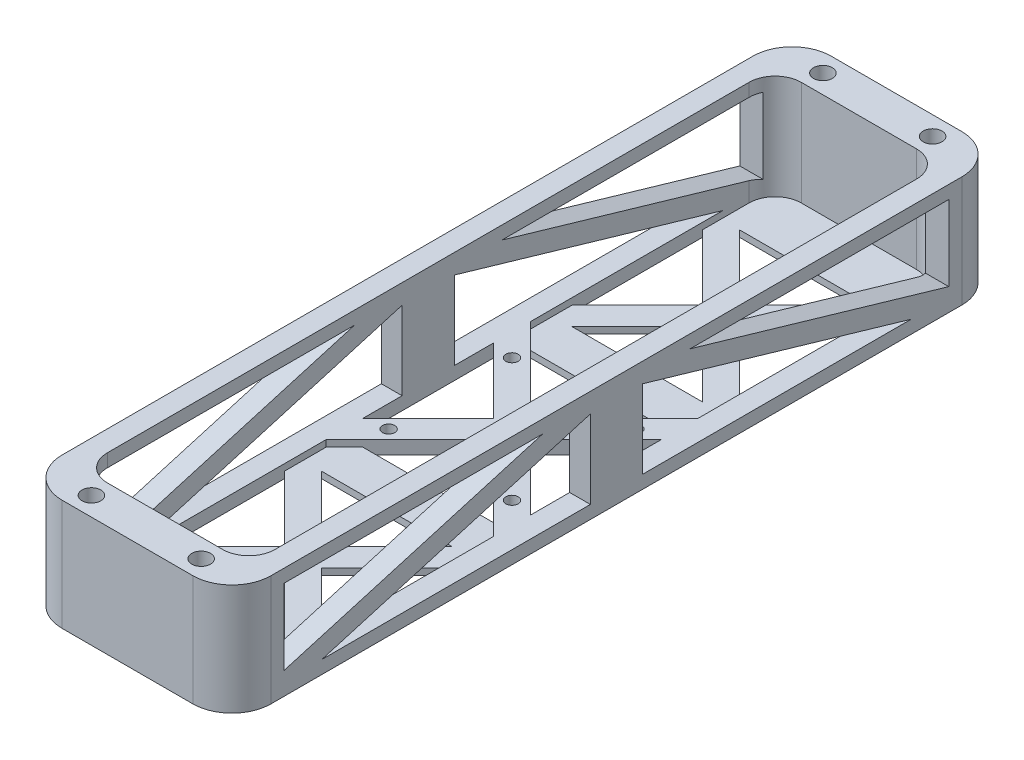
SolidWorks part; units mm, degrees
other "Markup1"
sketch "Sketch7" plane through (101.6, 15.875, -101.6) normal (0.5881, 0.7382, -0.3306) x (-0.8071, 0.509, -0.2992)
ref_plane "Front Plane" through (0, 0, 0) normal (0, 0, 1) x (1, 0, 0)
ref_plane "Top Plane" through (0, 0, 0) normal (0, 1, 0) x (1, 0, 0)
ref_plane "Right Plane" through (0, 0, 0) normal (1, 0, 0) x (0, 0, -1)
sketch "Sketch1" plane through (0, 0, 0) normal (0, 1, 0) x (1, 0, 0)
  line L0 (-25.4, 101.6) -> (25.4, 101.6)
  line L1 (-25.4, -101.6) -> (25.4, -101.6)
  line L2 (-101.6, -25.4) -> (-101.6, 25.4)
  line L3 (-25.4, 101.6) -> (25.4, 101.6)
  line L4 (101.6, -25.4) -> (101.6, 25.4)
  line L5 (-25.4, 101.6) -> (-25.4, 25.4)
  line L6 (-25.4, 25.4) -> (-101.6, 25.4)
  line L7 (101.6, -25.4) -> (101.6, 25.4)
  line L8 (-101.6, -25.4) -> (-101.6, 25.4)
  line L9 (-25.4, -101.6) -> (25.4, -101.6)
  line L10 (-101.6, -25.4) -> (-25.4, -25.4)
  line L11 (-25.4, -25.4) -> (-25.4, -101.6)
  line L12 (25.4, -101.6) -> (25.4, -25.4)
  line L13 (25.4, -25.4) -> (101.6, -25.4)
  line L14 (101.6, 25.4) -> (25.4, 25.4)
  line L15 (25.4, 25.4) -> (25.4, 101.6)
  line L16 (-13.335, 88.9) -> (13.335, 88.9)
  line L17 (88.9, -13.335) -> (88.9, 13.335)
  line L18 (-88.9, -13.335) -> (-88.9, 13.335)
  line L19 (-13.335, -88.9) -> (13.335, -88.9)
  line L21 (-19, -19) -> (19, -19)
  line L22 (-19, -19) -> (-19, 19)
  line L23 (-19, 19) -> (19, 19)
  line L24 (19, -19) -> (19, 19)
  line L25 (-19, -19) -> (19, 19) construction
  line L26 (-19, 19) -> (19, -19) construction
  circle A0 centre (-13.335, 88.9) radius 2.286
  circle A1 centre (13.335, 88.9) radius 2.286
  circle A2 centre (-13.335, -88.9) radius 2.286
  circle A3 centre (13.335, -88.9) radius 2.286
  circle A4 centre (88.9, -13.335) radius 2.286
  circle A5 centre (88.9, 13.335) radius 2.286
  circle A6 centre (-88.9, 13.335) radius 2.286
  circle A7 centre (-88.9, -13.335) radius 2.286
  circle A8 centre (-15, 15) radius 1.5
  circle A9 centre (15, 15) radius 1.5
  circle A10 centre (15, -15) radius 1.5
  circle A11 centre (-15, -15) radius 1.5
  point P0 (0, 0)
  point P6 (0, 101.6)
  point P7 (101.6, 0)
  point P9 (-101.6, 0)
  point P13 (0, 101.6)
  point P16 (101.6, 0)
  point P19 (-101.6, 0)
  point P22 (0, -101.6)
  point P41 (88.9, 0)
  point P43 (0, 0)
  point P44 (-88.9, 0)
  point P47 (0, -88.9)
  point P50 (0, 88.9)
  dimension "D4" = 4.572
  dimension "D14" = 3
  dimension "D1" = 203.2
  dimension "D2" = 50.8
  dimension "D3" = 203.2
  dimension "D5" = 26.67
  dimension "D6" = 12.7
  dimension "D7" = 12.7
  dimension "D8" = 12.7
  dimension "D9" = 12.7
  dimension "D10" = 76.2
  dimension "D11" = 76.2
  dimension "D12" = 38
  dimension "D13" = 4
extrude "Boss-Extrude1" add sketch "Sketch1" along normal blind 1.5875 contours L14 L15 L0 L5 L6 L2 L10 L11 L1 L12 L13 L4 | L21 L24 L23 L22 A11 A10 A9 A8
sketch "Sketch3" plane through (0, 1.5875, 0) normal (0, 1, 0) x (1, 0, 0)
  line L0 (-25.4, 25.4) -> (-25.4, -25.4)
  line L1 (-25.4, -25.4) -> (25.4, -25.4)
  line L2 (25.4, 25.4) -> (25.4, -25.4)
  line L3 (25.4, 25.4) -> (-25.4, 25.4)
  line L4 (-76.2, 25.4) -> (-76.2, -25.4)
  line L5 (-76.2, -25.4) -> (76.2, -25.4)
  line L6 (76.2, -25.4) -> (76.2, 25.4)
  line L7 (25.4, 76.2) -> (-25.4, 76.2)
  line L8 (25.4, -76.2) -> (-25.4, -76.2)
  line L9 (0, 55.2901) -> (-15.875, 71.1651)
  line L10 (0, 55.2901) -> (-4.4901, 50.8)
  line L11 (-4.4901, 50.8) -> (0, 46.3099)
  line L12 (101.6, 25.4) -> (25.4, 25.4)
  line L13 (25.4, 25.4) -> (25.4, 101.6)
  line L14 (25.4, 101.6) -> (-25.4, 101.6)
  line L15 (-25.4, 101.6) -> (-25.4, 25.4)
  line L16 (-25.4, 25.4) -> (-101.6, 25.4)
  line L17 (-101.6, 25.4) -> (-101.6, -25.4)
  line L18 (-101.6, -25.4) -> (-25.4, -25.4)
  line L19 (-25.4, -25.4) -> (-25.4, -101.6)
  line L20 (-25.4, -101.6) -> (25.4, -101.6)
  line L21 (25.4, -101.6) -> (25.4, -25.4)
  line L22 (25.4, -25.4) -> (101.6, -25.4)
  line L23 (101.6, -25.4) -> (101.6, 25.4)
  line L24 (101.6, 25.4) -> (25.4, 25.4)
  line L25 (25.4, 25.4) -> (25.4, 101.6)
  line L26 (25.4, 101.6) -> (-25.4, 101.6)
  line L27 (-25.4, 101.6) -> (-25.4, 25.4)
  line L28 (-25.4, 25.4) -> (-101.6, 25.4)
  line L29 (-101.6, 25.4) -> (-101.6, -25.4)
  line L30 (-101.6, -25.4) -> (-25.4, -25.4)
  line L31 (-25.4, -25.4) -> (-25.4, -101.6)
  line L32 (-25.4, -101.6) -> (25.4, -101.6)
  line L33 (25.4, -101.6) -> (25.4, -25.4)
  line L34 (25.4, -25.4) -> (101.6, -25.4)
  line L35 (101.6, -25.4) -> (101.6, 25.4)
  line L36 (0, 46.3099) -> (4.4901, 50.8)
  line L37 (4.4901, 50.8) -> (0, 55.2901)
  line L38 (-15.875, 71.1651) -> (15.875, 71.1651)
  line L39 (15.875, 71.1651) -> (0, 55.2901)
  line L43 (4.4901, 50.8) -> (20.3651, 66.675)
  line L44 (20.3651, 66.675) -> (20.3651, 34.925)
  line L45 (20.3651, 34.925) -> (4.4901, 50.8)
  line L46 (0, 46.3099) -> (15.875, 30.4349)
  line L47 (15.875, 30.4349) -> (-15.875, 30.4349)
  line L48 (-15.875, 30.4349) -> (0, 46.3099)
  line L49 (-4.4901, 50.8) -> (-20.3651, 34.925)
  line L50 (-20.3651, 34.925) -> (-20.3651, 66.675)
  line L51 (-20.3651, 66.675) -> (-4.4901, 50.8)
  line L52 (55.2901, 0) -> (71.1651, 15.875)
  line L53 (71.1651, 15.875) -> (71.1651, -15.875)
  line L54 (71.1651, -15.875) -> (55.2901, 0)
  line L55 (50.8, 4.4901) -> (34.925, 20.3651)
  line L56 (34.925, 20.3651) -> (66.675, 20.3651)
  line L57 (66.675, 20.3651) -> (50.8, 4.4901)
  line L58 (46.3099, 0) -> (30.4349, -15.875)
  line L59 (30.4349, -15.875) -> (30.4349, 15.875)
  line L60 (30.4349, 15.875) -> (46.3099, 0)
  line L61 (50.8, -4.4901) -> (66.675, -20.3651)
  line L62 (66.675, -20.3651) -> (34.925, -20.3651)
  line L63 (34.925, -20.3651) -> (50.8, -4.4901)
  line L64 (55.2901, 0) -> (50.8, 4.4901)
  line L65 (50.8, 4.4901) -> (46.3099, 0)
  line L66 (46.3099, 0) -> (50.8, -4.4901)
  line L67 (50.8, -4.4901) -> (55.2901, 0)
  line L68 (0, -55.2901) -> (15.875, -71.1651)
  line L69 (15.875, -71.1651) -> (-15.875, -71.1651)
  line L70 (-15.875, -71.1651) -> (0, -55.2901)
  line L71 (4.4901, -50.8) -> (20.3651, -34.925)
  line L72 (20.3651, -34.925) -> (20.3651, -66.675)
  line L73 (20.3651, -66.675) -> (4.4901, -50.8)
  line L74 (0, -46.3099) -> (-15.875, -30.4349)
  line L75 (-15.875, -30.4349) -> (15.875, -30.4349)
  line L76 (15.875, -30.4349) -> (0, -46.3099)
  line L77 (-4.4901, -50.8) -> (-20.3651, -66.675)
  line L78 (-20.3651, -66.675) -> (-20.3651, -34.925)
  line L79 (-20.3651, -34.925) -> (-4.4901, -50.8)
  line L80 (0, -55.2901) -> (4.4901, -50.8)
  line L81 (4.4901, -50.8) -> (0, -46.3099)
  line L82 (0, -46.3099) -> (-4.4901, -50.8)
  line L83 (-4.4901, -50.8) -> (0, -55.2901)
  line L84 (-55.2901, 0) -> (-71.1651, -15.875)
  line L85 (-71.1651, -15.875) -> (-71.1651, 15.875)
  line L86 (-71.1651, 15.875) -> (-55.2901, 0)
  line L87 (-50.8, -4.4901) -> (-34.925, -20.3651)
  line L88 (-34.925, -20.3651) -> (-66.675, -20.3651)
  line L89 (-66.675, -20.3651) -> (-50.8, -4.4901)
  line L90 (-46.3099, 0) -> (-30.4349, 15.875)
  line L91 (-30.4349, 15.875) -> (-30.4349, -15.875)
  line L92 (-30.4349, -15.875) -> (-46.3099, 0)
  line L93 (-50.8, 4.4901) -> (-66.675, 20.3651)
  line L94 (-66.675, 20.3651) -> (-34.925, 20.3651)
  line L95 (-34.925, 20.3651) -> (-50.8, 4.4901)
  line L96 (-55.2901, 0) -> (-50.8, -4.4901)
  line L97 (-50.8, -4.4901) -> (-46.3099, 0)
  line L98 (-46.3099, 0) -> (-50.8, 4.4901)
  line L99 (-50.8, 4.4901) -> (-55.2901, 0)
  line L100 (15.875, 20.3651) -> (0, 4.4901)
  line L101 (0, 4.4901) -> (-4.4901, 0)
  line L102 (4.4901, 0) -> (20.3651, 15.875)
  line L103 (0, -4.4901) -> (4.4901, 0)
  line L104 (-20.3651, -15.875) -> (-20.3651, 15.875)
  line L105 (-20.3651, 15.875) -> (-4.4901, 0)
  line L106 (15.875, -20.3651) -> (-15.875, -20.3651)
  line L107 (-15.875, 20.3651) -> (15.875, 20.3651)
  line L108 (0, -4.4901) -> (15.875, -20.3651)
  line L109 (20.3651, -15.875) -> (4.4901, 0)
  line L110 (20.3651, 15.875) -> (20.3651, -15.875)
  line L111 (4.4901, 0) -> (0, 4.4901)
  line L112 (-4.4901, 0) -> (-20.3651, -15.875)
  line L113 (-4.4901, 0) -> (0, -4.4901)
  line L114 (0, 4.4901) -> (-15.875, 20.3651)
  line L115 (-15.875, -20.3651) -> (0, -4.4901)
  circle A0 centre (0, 50.8) radius 3.175 construction
  circle A1 centre (50.8, 0) radius 3.175 construction
  circle A2 centre (0, -50.8) radius 3.175 construction
  circle A3 centre (-50.8, 0) radius 3.175 construction
  circle A4 centre (0, 0) radius 3.175 construction
  point P18 (-50.8, 0)
  point P20 (0, 50.8)
  point P22 (50.8, 0)
  point P23 (0, -50.8)
  point P24 (-101.6, 0)
  point P25 (0, 101.6)
  point P26 (101.6, 0)
  point P27 (0, -101.6)
  point P48 (0, 50.8)
  point P100 (0, 0)
  dimension "D2" = 25.4
  dimension "D3" = 25.4
  dimension "D4" = 25.4
  dimension "D5" = 25.4
  dimension "D6" = 25.4
  dimension "D7" = 25.4
  dimension "D8" = 25.4
  dimension "D9" = 25.4
  dimension "D10" = 6.35
  dimension "D11" = 31.75
  dimension "D12" = 45
  dimension "D13" = 4
  dimension "D14" = 4
  dimension "D1" = 0
extrude "Cut-Extrude1" cut sketch "Sketch3" against normal up to next contours L39 L38 L9 | L51 L50 L49 | L48 L47 L46 | L45 L44 L43 | L95 L94 L93 | L86 L85 L84 | L89 L88 L87 | L92 L91 L90 | L60 L59 L58 | L57 L56 L55 | L54 L53 L52 | L63 L62 L61 | L76 L75 L74 | L79 L78 L77 | L73 L72 L71 | L70 L69 L68 | L114 L100 L107 | L112 L105 L104 | L115 L106 L108 | L110 L102 L109
sketch "Sketch4" plane through (0, 1.5875, 0) normal (0, 1, 0) x (1, 0, 0)
  line L0 (-93.472, 13.335) -> (-93.472, -13.335)
  line L1 (-84.328, 13.335) -> (-84.328, -13.335)
  line L2 (-93.472, 13.335) -> (-93.472, 25.4)
  line L4 (-93.472, 25.4) -> (-84.328, 25.4)
  line L5 (-84.328, 20.3651) -> (-84.328, 13.335)
  line L6 (-84.328, -13.335) -> (-84.328, -20.3651)
  line L7 (-13.335, -84.328) -> (13.335, -84.328)
  line L8 (-13.335, -93.472) -> (13.335, -93.472)
  line L10 (-84.328, -25.4) -> (-93.472, -25.4)
  line L12 (101.6, 25.4) -> (25.4, 25.4)
  line L13 (25.4, 25.4) -> (25.4, 101.6)
  line L14 (25.4, 101.6) -> (-25.4, 101.6)
  line L15 (-25.4, 101.6) -> (-25.4, 25.4)
  line L16 (-25.4, 25.4) -> (-101.6, 25.4)
  line L17 (-101.6, 25.4) -> (-101.6, -25.4)
  line L18 (-101.6, -25.4) -> (-25.4, -25.4)
  line L19 (-25.4, -25.4) -> (-25.4, -101.6)
  line L20 (-25.4, -101.6) -> (25.4, -101.6)
  line L21 (25.4, -101.6) -> (25.4, -25.4)
  line L22 (25.4, -25.4) -> (101.6, -25.4)
  line L23 (101.6, -25.4) -> (101.6, 25.4)
  line L24 (101.6, 25.4) -> (25.4, 25.4)
  line L25 (25.4, 25.4) -> (25.4, 101.6)
  line L26 (25.4, 101.6) -> (-25.4, 101.6)
  line L27 (-25.4, 101.6) -> (-25.4, 25.4)
  line L28 (-25.4, 25.4) -> (-101.6, 25.4)
  line L29 (-101.6, 25.4) -> (-101.6, -25.4)
  line L30 (-101.6, -25.4) -> (-25.4, -25.4)
  line L31 (-25.4, -25.4) -> (-25.4, -101.6)
  line L32 (-25.4, -101.6) -> (25.4, -101.6)
  line L33 (25.4, -101.6) -> (25.4, -25.4)
  line L34 (25.4, -25.4) -> (101.6, -25.4)
  line L35 (101.6, -25.4) -> (101.6, 25.4)
  line L36 (84.328, -13.335) -> (84.328, 13.335)
  line L37 (93.472, -13.335) -> (93.472, 13.335)
  line L38 (-93.472, -25.4) -> (-93.472, -13.335)
  line L39 (-13.335, 93.472) -> (-25.4, 93.472)
  line L40 (-25.4, 93.472) -> (-25.4, 84.328)
  line L41 (13.335, 84.328) -> (-13.335, 84.328)
  line L42 (13.335, 93.472) -> (-13.335, 93.472)
  line L43 (-20.3651, 84.328) -> (-13.335, 84.328)
  line L44 (13.335, 84.328) -> (20.3651, 84.328)
  line L45 (25.4, 84.328) -> (25.4, 93.472)
  line L46 (25.4, 93.472) -> (13.335, 93.472)
  line L47 (84.328, 13.335) -> (84.328, 20.3651)
  line L48 (84.328, 25.4) -> (93.472, 25.4)
  line L49 (93.472, 25.4) -> (93.472, 13.335)
  line L50 (84.328, 25.4) -> (93.472, 25.4)
  line L51 (93.472, -13.335) -> (93.472, -25.4)
  line L52 (93.472, -25.4) -> (84.328, -25.4)
  line L53 (84.328, -20.3651) -> (84.328, -13.335)
  line L54 (13.335, -93.472) -> (25.4, -93.472)
  line L55 (25.4, -93.472) -> (25.4, -84.328)
  line L56 (20.3651, -84.328) -> (13.335, -84.328)
  line L59 (-13.335, -84.328) -> (-20.3651, -84.328)
  line L60 (-25.4, -84.328) -> (-25.4, -93.472)
  line L61 (-25.4, -93.472) -> (-13.335, -93.472)
  line L62 (20.3651, -34.925) -> (20.3651, -66.675) construction
  line L63 (-20.3651, -66.675) -> (-20.3651, -34.925) construction
  line L64 (-20.3651, 34.925) -> (-20.3651, 66.675) construction
  line L65 (20.3651, 66.675) -> (20.3651, 34.925) construction
  line L66 (34.925, 20.3651) -> (66.675, 20.3651) construction
  line L67 (66.675, -20.3651) -> (34.925, -20.3651) construction
  line L68 (-34.925, -20.3651) -> (-66.675, -20.3651) construction
  line L69 (-66.675, 20.3651) -> (-34.925, 20.3651) construction
  line L70 (20.3651, -34.925) -> (20.3651, -66.675)
  line L71 (-20.3651, -66.675) -> (-20.3651, -34.925)
  line L72 (-20.3651, 34.925) -> (-20.3651, 66.675)
  line L73 (20.3651, 66.675) -> (20.3651, 34.925)
  line L74 (34.925, 20.3651) -> (66.675, 20.3651)
  line L75 (66.675, -20.3651) -> (34.925, -20.3651)
  line L76 (-34.925, -20.3651) -> (-66.675, -20.3651)
  line L77 (-66.675, 20.3651) -> (-34.925, 20.3651)
  line L78 (-25.4, 20.3651) -> (-34.925, 20.3651)
  line L79 (-66.675, 20.3651) -> (-84.328, 20.3651)
  line L80 (-25.4, -20.3651) -> (-20.3651, -20.3651)
  line L81 (-20.3651, -20.3651) -> (-20.3651, -25.4)
  line L82 (-20.3651, 25.4) -> (-20.3651, 34.925)
  line L83 (-20.3651, 66.675) -> (-20.3651, 84.328)
  line L84 (20.3651, 84.328) -> (20.3651, 66.675)
  line L85 (20.3651, 34.925) -> (20.3651, 25.4)
  line L86 (20.3651, -25.4) -> (20.3651, -20.3651)
  line L87 (20.3651, -20.3651) -> (25.4, -20.3651)
  line L88 (25.4, 20.3651) -> (34.925, 20.3651)
  line L89 (66.675, 20.3651) -> (84.328, 20.3651)
  line L90 (84.328, -20.3651) -> (66.675, -20.3651)
  line L91 (34.925, -20.3651) -> (25.4, -20.3651)
  line L92 (20.3651, 25.4) -> (20.3651, 20.3651)
  line L93 (20.3651, -34.925) -> (20.3651, -25.4)
  line L94 (20.3651, 20.3651) -> (25.4, 20.3651)
  line L95 (20.3651, -66.675) -> (20.3651, -84.328)
  line L96 (-20.3651, -66.675) -> (-20.3651, -84.328)
  line L97 (-20.3651, -34.925) -> (-20.3651, -25.4)
  line L98 (-25.4, 20.3651) -> (-20.3651, 20.3651)
  line L99 (-20.3651, 20.3651) -> (-20.3651, 25.4)
  line L100 (-25.4, -20.3651) -> (-34.925, -20.3651)
  line L101 (-66.675, -20.3651) -> (-84.328, -20.3651)
  circle A0 centre (-88.9, -13.335) radius 2.286 construction
  circle A1 centre (-88.9, 13.335) radius 2.286 construction
  circle A2 centre (-88.9, -13.335) radius 2.286
  circle A3 centre (-88.9, 13.335) radius 2.286
  circle A7 centre (13.335, -88.9) radius 2.286
  circle A9 centre (-13.335, -88.9) radius 2.286
  arc A10 (93.472, 13.335) -> (84.328, 13.335) centre (88.9, 13.335) ccw
  circle A11 centre (88.9, 13.335) radius 2.286
  circle A13 centre (88.9, -13.335) radius 2.286
  circle A15 centre (-13.335, 88.9) radius 2.286
  circle A17 centre (13.335, 88.9) radius 2.286
  point P28 (0, 0)
  point P75 (0, 0)
  dimension "D1" = 0
  dimension "D4" = 4
extrude "Boss-Extrude4" add sketch "Sketch4" along normal blind 25.4
sketch "Sketch16" plane through (0, 1.5875, 0) normal (0, 1, 0) x (1, 0, 0)
  line L0 (15.875, 20.3651) -> (0, 4.4901) construction
  line L1 (0, 4.4901) -> (-15.875, 20.3651) construction
  line L2 (-15.875, 20.3651) -> (15.875, 20.3651) construction
  line L3 (20.3651, 15.875) -> (20.3651, -15.875) construction
  line L4 (4.4901, 0) -> (20.3651, 15.875) construction
  line L5 (20.3651, -15.875) -> (4.4901, 0) construction
  line L6 (15.875, -20.3651) -> (-15.875, -20.3651) construction
  line L7 (0, -4.4901) -> (15.875, -20.3651) construction
  line L8 (-15.875, -20.3651) -> (0, -4.4901) construction
  line L9 (-4.4901, 0) -> (-20.3651, -15.875) construction
  line L10 (-20.3651, -15.875) -> (-20.3651, 15.875) construction
  line L11 (-20.3651, 15.875) -> (-4.4901, 0) construction
  line L12 (15.875, 20.3651) -> (0, 4.4901)
  line L13 (0, 4.4901) -> (-15.875, 20.3651)
  line L14 (-15.875, 20.3651) -> (15.875, 20.3651)
  line L15 (20.3651, 15.875) -> (20.3651, -15.875)
  line L16 (4.4901, 0) -> (20.3651, 15.875)
  line L17 (20.3651, -15.875) -> (4.4901, 0)
  line L18 (15.875, -20.3651) -> (-15.875, -20.3651)
  line L19 (0, -4.4901) -> (15.875, -20.3651)
  line L20 (-15.875, -20.3651) -> (0, -4.4901)
  line L21 (-4.4901, 0) -> (-20.3651, -15.875)
  line L22 (-20.3651, -15.875) -> (-20.3651, 15.875)
  line L23 (-20.3651, 15.875) -> (-4.4901, 0)
  line L24 (-20.3651, 15.875) -> (-24.8553, 20.3651)
  line L25 (-15.875, 20.3651) -> (-20.3651, 24.8553)
  line L26 (15.875, 20.3651) -> (20.3651, 24.8553)
  line L27 (20.3651, 15.875) -> (24.8553, 20.3651)
  line L28 (15.875, -20.3651) -> (20.3651, -24.8553)
  line L29 (20.3651, -15.875) -> (24.8553, -20.3651)
  line L30 (-20.3651, -15.875) -> (-24.8553, -20.3651)
  line L31 (-15.875, -20.3651) -> (-20.3651, -24.8553)
  line L36 (84.328, -20.3651) -> (84.328, 20.3651)
  line L38 (84.328, -20.3651) -> (84.328, 20.3651)
  line L40 (84.328, 20.3651) -> (66.675, 20.3651)
  line L42 (84.328, 20.3651) -> (66.675, 20.3651)
  line L44 (66.675, 20.3651) -> (50.8, 4.4901)
  line L46 (66.675, 20.3651) -> (50.8, 4.4901)
  line L48 (50.8, 4.4901) -> (34.925, 20.3651)
  line L50 (50.8, 4.4901) -> (34.925, 20.3651)
  line L52 (34.925, 20.3651) -> (20.3651, 20.3651)
  line L54 (34.925, 20.3651) -> (20.3651, 20.3651)
  line L56 (20.3651, 20.3651) -> (20.3651, 34.925)
  line L58 (20.3651, 20.3651) -> (20.3651, 34.925)
  line L128 (20.3651, 34.925) -> (4.4901, 50.8)
  line L129 (20.3651, 34.925) -> (4.4901, 50.8)
  line L130 (4.4901, 50.8) -> (20.3651, 66.675)
  line L131 (4.4901, 50.8) -> (20.3651, 66.675)
  line L132 (20.3651, 66.675) -> (20.3651, 84.328)
  line L133 (20.3651, 66.675) -> (20.3651, 84.328)
  line L134 (20.3651, 84.328) -> (-20.3651, 84.328)
  line L135 (20.3651, 84.328) -> (-20.3651, 84.328)
  line L136 (-20.3651, 84.328) -> (-20.3651, 66.675)
  line L137 (-20.3651, 84.328) -> (-20.3651, 66.675)
  line L138 (-20.3651, 66.675) -> (-4.4901, 50.8)
  line L139 (-20.3651, 66.675) -> (-4.4901, 50.8)
  line L140 (-4.4901, 50.8) -> (-20.3651, 34.925)
  line L141 (-4.4901, 50.8) -> (-20.3651, 34.925)
  line L142 (-20.3651, 34.925) -> (-20.3651, 20.3651)
  line L143 (-20.3651, 34.925) -> (-20.3651, 20.3651)
  line L144 (-20.3651, 20.3651) -> (-34.925, 20.3651)
  line L145 (-20.3651, 20.3651) -> (-34.925, 20.3651)
  line L146 (-34.925, 20.3651) -> (-50.8, 4.4901)
  line L147 (-34.925, 20.3651) -> (-50.8, 4.4901)
  line L148 (-50.8, 4.4901) -> (-66.675, 20.3651)
  line L149 (-50.8, 4.4901) -> (-66.675, 20.3651)
  line L150 (-66.675, 20.3651) -> (-84.328, 20.3651)
  line L151 (-66.675, 20.3651) -> (-84.328, 20.3651)
  line L152 (-84.328, 20.3651) -> (-84.328, -20.3651)
  line L153 (-84.328, 20.3651) -> (-84.328, -20.3651)
  line L154 (-84.328, -20.3651) -> (-66.675, -20.3651)
  line L155 (-84.328, -20.3651) -> (-66.675, -20.3651)
  line L156 (-66.675, -20.3651) -> (-50.8, -4.4901)
  line L157 (-66.675, -20.3651) -> (-50.8, -4.4901)
  line L158 (-50.8, -4.4901) -> (-34.925, -20.3651)
  line L159 (-50.8, -4.4901) -> (-34.925, -20.3651)
  line L160 (-34.925, -20.3651) -> (-20.3651, -20.3651)
  line L161 (-34.925, -20.3651) -> (-20.3651, -20.3651)
  line L162 (-20.3651, -20.3651) -> (-20.3651, -34.925)
  line L163 (-20.3651, -20.3651) -> (-20.3651, -34.925)
  line L164 (-20.3651, -34.925) -> (-4.4901, -50.8)
  line L165 (-20.3651, -34.925) -> (-4.4901, -50.8)
  line L166 (-4.4901, -50.8) -> (-20.3651, -66.675)
  line L167 (-4.4901, -50.8) -> (-20.3651, -66.675)
  line L168 (-20.3651, -66.675) -> (-20.3651, -84.328)
  line L169 (-20.3651, -66.675) -> (-20.3651, -84.328)
  line L170 (-20.3651, -84.328) -> (20.3651, -84.328)
  line L171 (-20.3651, -84.328) -> (20.3651, -84.328)
  line L172 (20.3651, -84.328) -> (20.3651, -66.675)
  line L173 (20.3651, -84.328) -> (20.3651, -66.675)
  line L174 (20.3651, -66.675) -> (4.4901, -50.8)
  line L175 (20.3651, -66.675) -> (4.4901, -50.8)
  line L176 (4.4901, -50.8) -> (20.3651, -34.925)
  line L177 (4.4901, -50.8) -> (20.3651, -34.925)
  line L178 (20.3651, -34.925) -> (20.3651, -20.3651)
  line L179 (20.3651, -34.925) -> (20.3651, -20.3651)
  line L180 (20.3651, -20.3651) -> (34.925, -20.3651)
  line L181 (20.3651, -20.3651) -> (34.925, -20.3651)
  line L182 (34.925, -20.3651) -> (50.8, -4.4901)
  line L183 (34.925, -20.3651) -> (50.8, -4.4901)
  line L184 (50.8, -4.4901) -> (66.675, -20.3651)
  line L185 (50.8, -4.4901) -> (66.675, -20.3651)
  line L186 (66.675, -20.3651) -> (84.328, -20.3651)
  line L187 (66.675, -20.3651) -> (84.328, -20.3651)
  circle A0 centre (-15, 15) radius 1.5 construction
  circle A1 centre (-15, -15) radius 1.5 construction
  circle A2 centre (15, -15) radius 1.5 construction
  circle A3 centre (15, 15) radius 1.5 construction
  circle A4 centre (-15, 15) radius 1.5
  circle A5 centre (-15, -15) radius 1.5
  circle A6 centre (15, -15) radius 1.5
  circle A7 centre (15, 15) radius 1.5
  dimension "D1" = 0
extrude "Boss-Extrude6" add sketch "Sketch16" along normal blind 1.5875 contours L179 L181 L29 L17 L16 L27 L54 L58 L26 L12 L13 L25 L143 L145 L24 L23 L21 L30 L161 L163 L31 L20 L19 L28
sketch "Sketch17" plane through (0, 26.9875, 0) normal (0, 1, 0) x (1, 0, 0)
  line L0 (-20.3651, -20.3651) -> (-20.3651, -84.328) construction
  line L1 (-84.328, -20.3651) -> (-20.3651, -20.3651) construction
  line L2 (84.328, -20.3651) -> (20.3651, -20.3651) construction
  line L3 (20.3651, -84.328) -> (20.3651, -20.3651) construction
  line L4 (20.3651, 84.328) -> (20.3651, 20.3651) construction
  line L5 (20.3651, 20.3651) -> (84.328, 20.3651) construction
  line L6 (-20.3651, 20.3651) -> (-20.3651, 84.328) construction
  line L7 (-20.3651, 20.3651) -> (-84.328, 20.3651) construction
  line L8 (-4.4901, 0) -> (-24.8553, -20.3651) construction
  line L9 (0, -4.4901) -> (-20.3651, -24.8553) construction
  line L10 (0, -4.4901) -> (20.3651, -24.8553) construction
  line L11 (4.4901, 0) -> (24.8553, -20.3651) construction
  line L12 (-25.4, -25.4) -> (-25.4, -93.472)
  line L13 (-25.4, -93.472) -> (25.4, -93.472)
  line L14 (25.4, -93.472) -> (25.4, -25.4)
  line L15 (25.4, -25.4) -> (93.472, -25.4)
  line L16 (93.472, -25.4) -> (93.472, 25.4)
  line L17 (93.472, 25.4) -> (25.4, 25.4)
  line L18 (25.4, 25.4) -> (25.4, 93.472)
  line L19 (25.4, 93.472) -> (-25.4, 93.472)
  line L20 (-25.4, 93.472) -> (-25.4, 25.4)
  line L21 (-25.4, 25.4) -> (-93.472, 25.4)
  line L22 (-93.472, 25.4) -> (-93.472, -25.4)
  line L23 (-93.472, -25.4) -> (-25.4, -25.4)
  line L24 (-25.4, -25.4) -> (-25.4, -93.472)
  line L25 (-25.4, -93.472) -> (25.4, -93.472)
  line L26 (25.4, -93.472) -> (25.4, -25.4)
  line L27 (25.4, -25.4) -> (93.472, -25.4)
  line L28 (93.472, -25.4) -> (93.472, 25.4)
  line L29 (93.472, 25.4) -> (25.4, 25.4)
  line L30 (25.4, 25.4) -> (25.4, 93.472)
  line L31 (25.4, 93.472) -> (-25.4, 93.472)
  line L32 (-25.4, 93.472) -> (-25.4, 25.4)
  line L33 (-25.4, 25.4) -> (-93.472, 25.4)
  line L34 (-93.472, 25.4) -> (-93.472, -25.4)
  line L35 (-93.472, -25.4) -> (-25.4, -25.4)
  line L36 (4.4901, 0) -> (24.8553, 20.3651) construction
  line L37 (0, 4.4901) -> (20.3651, 24.8553) construction
  line L38 (0, 4.4901) -> (-20.3651, 24.8553) construction
  line L39 (-4.4901, 0) -> (-24.8553, 20.3651) construction
  line L40 (-20.3651, -20.3651) -> (-20.3651, -84.328)
  line L41 (-84.328, -20.3651) -> (-20.3651, -20.3651)
  line L42 (84.328, -20.3651) -> (20.3651, -20.3651)
  line L43 (20.3651, -84.328) -> (20.3651, -20.3651)
  line L44 (20.3651, 84.328) -> (20.3651, 20.3651)
  line L45 (20.3651, 20.3651) -> (84.328, 20.3651)
  line L46 (-20.3651, 20.3651) -> (-20.3651, 84.328)
  line L47 (-20.3651, 20.3651) -> (-84.328, 20.3651)
  line L48 (-4.4901, 0) -> (-24.8553, -20.3651)
  line L49 (0, -4.4901) -> (-20.3651, -24.8553)
  line L50 (0, -4.4901) -> (20.3651, -24.8553)
  line L51 (4.4901, 0) -> (24.8553, -20.3651)
  line L52 (4.4901, 0) -> (24.8553, 20.3651)
  line L53 (0, 4.4901) -> (20.3651, 24.8553)
  line L54 (0, 4.4901) -> (-20.3651, 24.8553)
  line L55 (-4.4901, 0) -> (-24.8553, 20.3651)
  line L56 (-24.8553, 20.3651) -> (-29.8901, 25.4)
  line L57 (-20.3651, 24.8553) -> (-25.4, 29.8901)
  line L58 (20.3651, 24.8553) -> (25.4, 29.8901)
  line L59 (24.8553, 20.3651) -> (29.8901, 25.4)
  line L60 (24.8553, -20.3651) -> (29.8901, -25.4)
  line L61 (20.3651, -24.8553) -> (25.4, -29.8901)
  line L62 (-24.8553, -20.3651) -> (-29.8901, -25.4)
  line L63 (-20.3651, -24.8553) -> (-25.4, -29.8901)
  line L64 (-29.8901, 25.4) -> (-29.8901, 20.3651)
  line L65 (-29.8901, 20.3651) -> (-24.8553, 20.3651)
  line L66 (-25.4, 29.8901) -> (-20.3651, 29.8901)
  line L67 (-20.3651, 29.8901) -> (-20.3651, 24.8553)
  line L68 (25.4, 29.8901) -> (20.3651, 29.8901)
  line L69 (20.3651, 29.8901) -> (20.3651, 24.8553)
  line L70 (24.8553, 20.3651) -> (29.8901, 20.3651)
  line L71 (29.8901, 20.3651) -> (29.8901, 25.4)
  line L72 (25.4, -29.8901) -> (20.3651, -29.8901)
  line L73 (20.3651, -29.8901) -> (20.3651, -24.8553)
  line L74 (24.8553, -20.3651) -> (29.8901, -20.3651)
  line L75 (29.8901, -20.3651) -> (29.8901, -25.4)
  line L76 (-24.8553, -20.3651) -> (-29.8901, -20.3651)
  line L77 (-29.8901, -20.3651) -> (-29.8901, -25.4)
  line L78 (-25.4, -29.8901) -> (-20.3651, -29.8901)
  line L79 (-20.3651, -29.8901) -> (-20.3651, -24.8553)
  line M23 (20.3651, 20.3651) -> (84.328, 20.3651)
  line M26 (20.3651, -20.3651) -> (20.3651, -84.328)
  line M29 (-20.3651, -20.3651) -> (-84.328, -20.3651)
  line M32 (-20.3651, 20.3651) -> (-20.3651, 84.328)
  line M43 (-25.4, -25.4) -> (-25.4, -93.472)
  line M46 (25.4, -25.4) -> (93.472, -25.4)
  line M49 (25.4, 25.4) -> (25.4, 93.472)
  line M52 (-25.4, 25.4) -> (-93.472, 25.4)
  dimension "D1" = 0
extrude "Cut-Extrude13" cut sketch "Sketch17" against normal up to surface (23.8125 mm away) contours L57 L32 L56 L47 M32 M52 | L59 L29 L58 L44 M23 M49 | L61 L26 L60 L42 M26 M46 | L63 L40 L62 L35 M29 M43 | L56 L64 L47 | L66 L57 L46 | L58 L68 L44 | L45 L71 L59 | L75 L42 L60 | L72 L61 L43 | L63 L78 L40 | L41 L77 L62 up to face at (15, 3.175, -13.5)
sketch "Sketch18" plane through (0, 0, 25.4) normal (0, 0, 1) x (1, 0, 0)
  line L0 (84.328, 26.9875) -> (84.328, 1.5875) construction
  line L1 (-84.328, 26.9875) -> (-84.328, 1.5875) construction
  line L2 (84.328, 26.9875) -> (84.328, 1.5875)
  line L3 (-84.328, 26.9875) -> (-84.328, 1.5875)
  line L4 (-25.4, 1.5875) -> (25.4, 1.5875) construction
  line L8 (-25.4, 3.175) -> (-29.8901, 3.175)
  line L9 (-29.8901, 3.175) -> (-29.8901, 26.9875)
  line L10 (-29.8901, 26.9875) -> (-93.472, 26.9875)
  line L11 (-93.472, 26.9875) -> (-93.472, 1.5875)
  line L12 (-93.472, 1.5875) -> (-101.6, 1.5875)
  line L13 (-101.6, 1.5875) -> (-101.6, 0)
  line L14 (-101.6, 0) -> (-25.4, 0)
  line L15 (-25.4, 0) -> (-25.4, 3.175)
  line L16 (-25.4, 3.175) -> (-29.8901, 3.175)
  line L17 (-29.8901, 3.175) -> (-29.8901, 26.9875)
  line L18 (-29.8901, 26.9875) -> (-93.472, 26.9875)
  line L19 (-93.472, 26.9875) -> (-93.472, 1.5875)
  line L20 (-93.472, 1.5875) -> (-101.6, 1.5875)
  line L21 (-101.6, 1.5875) -> (-101.6, 0)
  line L22 (-101.6, 0) -> (-25.4, 0)
  line L23 (-25.4, 0) -> (-25.4, 3.175)
  line L24 (29.8901, 26.9875) -> (29.8901, 3.175)
  line L25 (29.8901, 3.175) -> (25.4, 3.175)
  line L26 (25.4, 3.175) -> (25.4, 0)
  line L27 (25.4, 0) -> (101.6, 0)
  line L28 (101.6, 0) -> (101.6, 1.5875)
  line L29 (101.6, 1.5875) -> (93.472, 1.5875)
  line L30 (93.472, 1.5875) -> (93.472, 26.9875)
  line L31 (93.472, 26.9875) -> (29.8901, 26.9875)
  line L32 (29.8901, 26.9875) -> (29.8901, 3.175)
  line L33 (29.8901, 3.175) -> (25.4, 3.175)
  line L34 (25.4, 3.175) -> (25.4, 0)
  line L35 (25.4, 0) -> (101.6, 0)
  line L36 (101.6, 0) -> (101.6, 1.5875)
  line L37 (101.6, 1.5875) -> (93.472, 1.5875)
  line L38 (93.472, 1.5875) -> (93.472, 26.9875)
  line L39 (93.472, 26.9875) -> (29.8901, 26.9875)
  spline S0 degree 2 poles (-77.978, 26.9875) (0.0091, -28.8428) (77.978, 26.9875) knots 0 0 0 1 1 1
  point P18 (-77.978, 26.9875)
  point P20 (77.978, 26.9875)
  point P22 (0, 1.5875)
  point P23 (0.04, -0.9276)
  point P28 (-29.8901, 3.175)
  dimension "D3" = 6.35
  dimension "D4" = 6.35
  dimension "D1" = 0
  dimension "D2" = 0
extrude "Cut-Extrude15" cut sketch "Sketch18" against normal up to surface (50.8 mm away) contours L1 S0 L0
sketch "Sketch20" plane through (0, 1.5875, 0) normal (0, 1, 0) x (1, 0, 0)
  line L0 (-93.472, -25.4) -> (-93.472, 25.4) construction
  line L1 (-93.472, 25.4) -> (-101.6, 25.4) construction
  line L2 (-101.6, 25.4) -> (-101.6, -25.4) construction
  line L3 (-101.6, -25.4) -> (-93.472, -25.4) construction
  line L4 (-25.4, 101.6) -> (-25.4, 93.472)
  line L5 (-25.4, 93.472) -> (25.4, 93.472)
  line L6 (25.4, 93.472) -> (25.4, 101.6)
  line L7 (25.4, 101.6) -> (-25.4, 101.6)
  line L8 (-25.4, 101.6) -> (-25.4, 93.472)
  line L9 (-25.4, 93.472) -> (25.4, 93.472)
  line L10 (25.4, 93.472) -> (25.4, 101.6)
  line L11 (25.4, 101.6) -> (-25.4, 101.6)
  line L12 (25.4, -101.6) -> (25.4, -93.472) construction
  line L13 (25.4, -93.472) -> (-25.4, -93.472) construction
  line L14 (-25.4, -93.472) -> (-25.4, -101.6) construction
  line L15 (-25.4, -101.6) -> (25.4, -101.6) construction
  line L16 (93.472, 25.4) -> (93.472, -25.4) construction
  line L17 (93.472, -25.4) -> (101.6, -25.4) construction
  line L18 (101.6, -25.4) -> (101.6, 25.4) construction
  line L19 (101.6, 25.4) -> (93.472, 25.4) construction
  line L20 (-93.472, -25.4) -> (-93.472, 25.4)
  line L21 (-93.472, 25.4) -> (-101.6, 25.4)
  line L22 (-101.6, 25.4) -> (-101.6, -25.4)
  line L23 (-101.6, -25.4) -> (-93.472, -25.4)
  line L24 (25.4, -101.6) -> (25.4, -93.472)
  line L25 (25.4, -93.472) -> (-25.4, -93.472)
  line L26 (-25.4, -93.472) -> (-25.4, -101.6)
  line L27 (-25.4, -101.6) -> (25.4, -101.6)
  line L28 (93.472, 25.4) -> (93.472, -25.4)
  line L29 (93.472, -25.4) -> (101.6, -25.4)
  line L30 (101.6, -25.4) -> (101.6, 25.4)
  line L31 (101.6, 25.4) -> (93.472, 25.4)
  dimension "D1" = 0
extrude "Cut-Extrude17" cut sketch "Sketch20" against normal up to next
fillet "Fillet2" radius 9.525 8 edges at (-25.4, 13.4937, -93.472) (25.4, 13.4937, -93.472) (93.472, 13.4937, -25.4) (93.472, 13.4937, 25.4) (25.4, 13.4937, 93.472) (-25.4, 13.4937, 93.472) (-93.472, 13.4937, -25.4) (-93.472, 13.4937, 25.4)
fillet "Fillet3" radius 6.35 8 edges at (-84.328, 14.2875, -20.3651) (-84.328, 14.2875, 20.3651) (-20.3651, 14.2875, 84.328) (20.3651, 14.2875, 84.328) (84.328, 14.2875, 20.3651) (84.328, 14.2875, -20.3651) (-20.3651, 14.2875, -84.328) (20.3651, 14.2875, -84.328)
mirror "Mirror1" about plane through (0, 0, 0) normal (1, 0, 0) of "Cut-Extrude15"
sketch "Sketch21" plane through (0, 0, 93.472) normal (0, 0, 1) x (1, 0, 0)
  line L0 (93.472, 26.9875) -> (83.947, 26.9875) construction
  line L1 (83.947, 0) -> (93.472, 0) construction
  line L2 (93.472, 0) -> (93.472, 26.9875) construction
  line L3 (29.8901, 3.175) -> (25.4, 3.175) construction
  line L4 (25.4, 3.175) -> (25.4, 0) construction
  line L5 (25.4, 0) -> (83.947, 0) construction
  line L6 (83.947, 26.9875) -> (77.978, 26.9875) construction
  line L7 (-83.947, 26.9875) -> (-93.472, 26.9875) construction
  line L8 (-93.472, 26.9875) -> (-93.472, 0) construction
  line L9 (-93.472, 0) -> (-83.947, 0) construction
  line L10 (-77.978, 26.9875) -> (-83.947, 26.9875) construction
  line L11 (-83.947, 0) -> (-25.4, 0) construction
  line L12 (-25.4, 0) -> (-25.4, 3.175) construction
  line L13 (-25.4, 3.175) -> (-29.8901, 3.175) construction
  line L14 (93.472, 26.9875) -> (83.947, 26.9875)
  line L15 (83.947, 0) -> (93.472, 0)
  line L16 (93.472, 0) -> (93.472, 26.9875)
  line L17 (29.8901, 3.175) -> (25.4, 3.175)
  line L18 (25.4, 3.175) -> (25.4, 0)
  line L19 (25.4, 0) -> (83.947, 0)
  line L20 (83.947, 26.9875) -> (77.978, 26.9875)
  line L21 (-83.947, 26.9875) -> (-93.472, 26.9875)
  line L22 (-93.472, 26.9875) -> (-93.472, 0)
  line L23 (-93.472, 0) -> (-83.947, 0)
  line L24 (-77.978, 26.9875) -> (-83.947, 26.9875)
  line L25 (-83.947, 0) -> (-25.4, 0)
  line L26 (-25.4, 0) -> (-25.4, 3.175)
  line L27 (-25.4, 3.175) -> (-29.8901, 3.175)
  parabola Q0 (77.978, 26.9875) -> (29.8901, 3.175) focus (-0.0134, 53.5282) apex (-0.0223, -0.9276) construction
  parabola Q1 (-29.8901, 3.175) -> (-77.978, 26.9875) focus (0.0134, 53.5282) apex (0.0223, -0.9276) construction
  parabola Q2 (77.978, 26.9875) -> (29.8901, 3.175) focus (-0.0134, 53.5282) apex (-0.0223, -0.9276)
  parabola Q3 (-29.8901, 3.175) -> (-77.978, 26.9875) focus (0.0134, 53.5282) apex (0.0223, -0.9276)
extrude "Cut-Extrude18" cut sketch "Sketch21" against normal up to surface (118.872 mm away) up to face at (50.4197, 8.0698, -25.4)
sketch "Sketch22" plane through (0, 1.5875, 0) normal (0, 1, 0) x (1, 0, 0)
  line L0 (25.4, -20.3651) -> (25.4, 20.3651) construction
  line L1 (25.4, 20.3651) -> (24.8553, 20.3651) construction
  line L2 (24.8553, 20.3651) -> (20.3651, 15.875) construction
  line L3 (20.3651, 15.875) -> (20.3651, -15.875) construction
  line L4 (20.3651, -15.875) -> (24.8553, -20.3651) construction
  line L5 (24.8553, -20.3651) -> (25.4, -20.3651) construction
  line L6 (-25.4, 20.3651) -> (-25.4, -20.3651) construction
  line L7 (-25.4, -20.3651) -> (-24.8553, -20.3651) construction
  line L8 (-24.8553, -20.3651) -> (-20.3651, -15.875) construction
  line L9 (-20.3651, -15.875) -> (-20.3651, 15.875) construction
  line L10 (-20.3651, 15.875) -> (-24.8553, 20.3651) construction
  line L11 (-24.8553, 20.3651) -> (-25.4, 20.3651) construction
  line L12 (25.4, -20.3651) -> (25.4, 20.3651)
  line L13 (25.4, 20.3651) -> (24.8553, 20.3651)
  line L14 (24.8553, 20.3651) -> (20.3651, 15.875)
  line L15 (20.3651, 15.875) -> (20.3651, -15.875)
  line L16 (20.3651, -15.875) -> (24.8553, -20.3651)
  line L17 (24.8553, -20.3651) -> (25.4, -20.3651)
  line L18 (-25.4, 20.3651) -> (-25.4, -20.3651)
  line L19 (-25.4, -20.3651) -> (-24.8553, -20.3651)
  line L20 (-24.8553, -20.3651) -> (-20.3651, -15.875)
  line L21 (-20.3651, -15.875) -> (-20.3651, 15.875)
  line L22 (-20.3651, 15.875) -> (-24.8553, 20.3651)
  line L23 (-24.8553, 20.3651) -> (-25.4, 20.3651)
extrude "Boss-Extrude7" add sketch "Sketch22" along normal up to surface (1.5875 mm away) up to face at (0, 3.175, 0)
sketch "Sketch23" plane through (0, 3.175, 0) normal (0, 1, 0) x (1, 0, 0)
  line L0 (4.4901, 0) -> (20.3651, -15.875) construction
  line L1 (4.4901, 0) -> (20.3651, 15.875) construction
  line L2 (-4.4901, 0) -> (-20.3651, -15.875) construction
  line L3 (-4.4901, 0) -> (-20.3651, 15.875) construction
  line L4 (4.4901, 0) -> (20.3651, -15.875)
  line L5 (4.4901, 0) -> (20.3651, 15.875)
  line L6 (-4.4901, 0) -> (-20.3651, -15.875)
  line L7 (-4.4901, 0) -> (-20.3651, 15.875)
  line L8 (-20.3651, 24.8553) -> (-20.3651, -24.8553)
  line L9 (20.3651, -24.8553) -> (20.3651, 24.8553)
  line L14 (-20.3651, 29.8901) -> (-25.4, 29.8901)
  line L15 (-25.4, 29.8901) -> (-25.4, -29.8901)
  line L16 (-20.3651, 29.8901) -> (-25.4, 29.8901)
  line L17 (-20.3651, -29.8901) -> (-20.3651, -24.8553)
  line L18 (-20.3651, -24.8553) -> (0, -4.4901)
  line L19 (0, -4.4901) -> (20.3651, -24.8553)
  line L20 (20.3651, -24.8553) -> (20.3651, -29.8901)
  line L21 (-25.4, -29.8901) -> (-20.3651, -29.8901)
  line L22 (25.4, -29.8901) -> (25.4, 29.8901)
  line L23 (-25.4, -29.8901) -> (-20.3651, -29.8901)
  line L24 (20.3651, 29.8901) -> (20.3651, 24.8553)
  line L25 (20.3651, 24.8553) -> (0, 4.4901)
  line L26 (0, 4.4901) -> (-20.3651, 24.8553)
  line L27 (-20.3651, 24.8553) -> (-20.3651, 29.8901)
  line L29 (-25.4, 29.8901) -> (-25.4, -29.8901)
  line L31 (-20.3651, -29.8901) -> (-20.3651, -24.8553)
  line L32 (-20.3651, -24.8553) -> (0, -4.4901)
  line L33 (0, -4.4901) -> (20.3651, -24.8553)
  line L34 (20.3651, -24.8553) -> (20.3651, -29.8901)
  line L36 (25.4, -29.8901) -> (25.4, 29.8901)
  line L38 (20.3651, 29.8901) -> (20.3651, 24.8553)
  line L39 (20.3651, 24.8553) -> (0, 4.4901)
  line L40 (0, 4.4901) -> (-20.3651, 24.8553)
  line L41 (-20.3651, 24.8553) -> (-20.3651, 29.8901)
  line L52 (20.3651, -29.8901) -> (25.4, -29.8901)
  line L53 (20.3651, -29.8901) -> (25.4, -29.8901)
  line L54 (25.4, 29.8901) -> (20.3651, 29.8901)
  line L55 (25.4, 29.8901) -> (20.3651, 29.8901)
  circle A0 centre (-15, -15) radius 1.5 construction
  circle A1 centre (15, -15) radius 1.5 construction
  circle A2 centre (15, 15) radius 1.5 construction
  circle A3 centre (-15, 15) radius 1.5 construction
  circle A4 centre (-15, -15) radius 1.5
  circle A5 centre (15, -15) radius 1.5
  circle A6 centre (15, 15) radius 1.5
  circle A7 centre (-15, 15) radius 1.5
  circle A8 centre (-15, 15) radius 3.175
  circle A9 centre (15, -15) radius 3.175
  circle A10 centre (15, 15) radius 3.175
  circle A11 centre (-15, -15) radius 3.175
  dimension "D1" = 0
extrude "Boss-Extrude8" add sketch "Sketch23" along normal blind 3.175
sketch "Sketch24" plane through (-25.4, 0, 0) normal (-1, 0, 0) x (0, 0, 1)
  line L0 (-29.8901, 26.9875) -> (29.8901, 26.9875)
  line L8 (29.8901, 6.35) -> (-29.8901, 6.35)
  line L9 (-29.8901, 6.35) -> (-29.8901, 26.9875)
  line L10 (-29.8901, 26.9875) -> (-83.947, 26.9875)
  line L11 (-83.947, 26.9875) -> (-83.947, 0)
  line L12 (-83.947, 0) -> (83.947, 0)
  line L13 (83.947, 0) -> (83.947, 26.9875)
  line L14 (83.947, 26.9875) -> (29.8901, 26.9875)
  line L15 (29.8901, 26.9875) -> (29.8901, 6.35)
  line L16 (29.8901, 6.35) -> (-29.8901, 6.35)
  line L17 (-29.8901, 6.35) -> (-29.8901, 26.9875)
  line L23 (29.8901, 26.9875) -> (29.8901, 6.35)
  line M9 (29.8901, 6.35) -> (-29.8901, 6.35)
  line M10 (-29.8901, 6.35) -> (-29.8901, 26.9875)
  line M16 (29.8901, 26.9875) -> (29.8901, 6.35)
  dimension "D1" = 0
extrude "Boss-Extrude9" add sketch "Sketch24" against normal up to surface (5.0349 mm away) contours L0 M10 M9 M16 up to face at (-20.3651, 6.0854, 0)
sketch "Sketch25" plane through (25.4, 0, 0) normal (1, 0, 0) x (0, 0, -1)
  line L0 (-29.8901, 26.9875) -> (29.8901, 26.9875)
  line L8 (29.8901, 26.9875) -> (29.8901, 6.35)
  line L9 (29.8901, 6.35) -> (-29.8901, 6.35)
  line L10 (-29.8901, 6.35) -> (-29.8901, 26.9875)
  line L11 (-29.8901, 26.9875) -> (-83.947, 26.9875)
  line L12 (-83.947, 26.9875) -> (-83.947, 0)
  line L13 (-83.947, 0) -> (83.947, 0)
  line L14 (83.947, 0) -> (83.947, 26.9875)
  line L15 (83.947, 26.9875) -> (29.8901, 26.9875)
  line L16 (29.8901, 26.9875) -> (29.8901, 6.35)
  line L17 (29.8901, 6.35) -> (-29.8901, 6.35)
  line L18 (-29.8901, 6.35) -> (-29.8901, 26.9875)
  line L19 (-29.8901, 26.9875) -> (-83.947, 26.9875)
  line L20 (-83.947, 26.9875) -> (-83.947, 0)
  line L21 (-83.947, 0) -> (83.947, 0)
  line L22 (83.947, 0) -> (83.947, 26.9875)
  line L23 (83.947, 26.9875) -> (29.8901, 26.9875)
  line M9 (29.8901, 26.9875) -> (29.8901, 6.35)
  line M10 (29.8901, 6.35) -> (-29.8901, 6.35)
  line M11 (-29.8901, 6.35) -> (-29.8901, 26.9875)
  dimension "D1" = 0
extrude "Boss-Extrude10" add sketch "Sketch25" against normal up to surface (5.0349 mm away) contours L0 M11 M10 M9 up to face at (20.3651, 6.0854, 0)
sketch "Sketch28" plane through (-25.4, 0, 0) normal (-1, 0, 0) x (0, 0, 1)
  line L0 (-80.772, 5.4657) -> (-17.9094, 23.8125)
  line L1 (-6.35, 0) -> (6.35, 0)
  line L2 (-6.35, 0) -> (-6.35, 26.9875)
  line L3 (-6.35, 26.9875) -> (6.35, 26.9875)
  line L4 (83.947, 26.9875) -> (-83.947, 26.9875)
  line L5 (-83.947, 26.9875) -> (-83.947, 0)
  line L6 (-83.947, 0) -> (83.947, 0)
  line L7 (83.947, 0) -> (83.947, 26.9875)
  line L8 (83.947, 26.9875) -> (-83.947, 26.9875)
  line L9 (-83.947, 26.9875) -> (-83.947, 0)
  line L10 (-83.947, 0) -> (83.947, 0)
  line L11 (83.947, 0) -> (83.947, 26.9875)
  line L12 (6.35, 0) -> (6.35, 26.9875)
  line L13 (-6.35, 0) -> (6.35, 26.9875) construction
  line L14 (-6.35, 26.9875) -> (6.35, 0) construction
  line L15 (-80.772, 3.175) -> (80.772, 3.175)
  line L16 (-80.772, 3.175) -> (-80.772, 23.8125)
  line L17 (-80.772, 23.8125) -> (80.772, 23.8125)
  line L18 (80.772, 3.175) -> (80.772, 23.8125)
  line L19 (-80.772, 3.175) -> (80.772, 23.8125) construction
  line L20 (-80.772, 23.8125) -> (80.772, 3.175) construction
  line L21 (-6.35, 22.225) -> (-71.6219, 3.175)
  line L22 (0, 13.4938) -> (0, 23.8125) construction
  line L23 (6.35, 22.225) -> (71.6219, 3.175)
  line L24 (80.772, 5.4657) -> (17.9094, 23.8125)
  point P2 (-83.947, 13.4937)
  point P4 (0, 13.4937)
  point P6 (0, 13.4937)
  point P10 (0, 13.4937)
  dimension "D2" = 12.7
  dimension "D3" = 3.175
  dimension "D4" = 3.175
  dimension "D5" = 4.7625
  dimension "D6" = 1.5875
  dimension "D1" = 0
extrude "Cut-Extrude21" cut sketch "Sketch28" against normal up to surface (45.7651 mm away) contours L17 L16 L0 | L2 L21 L15 | L23 L12 L15 | L24 L18 L17
mirror "Mirror4" about plane through (0, 0, 0) normal (1, 0, 0) of "Cut-Extrude21"
